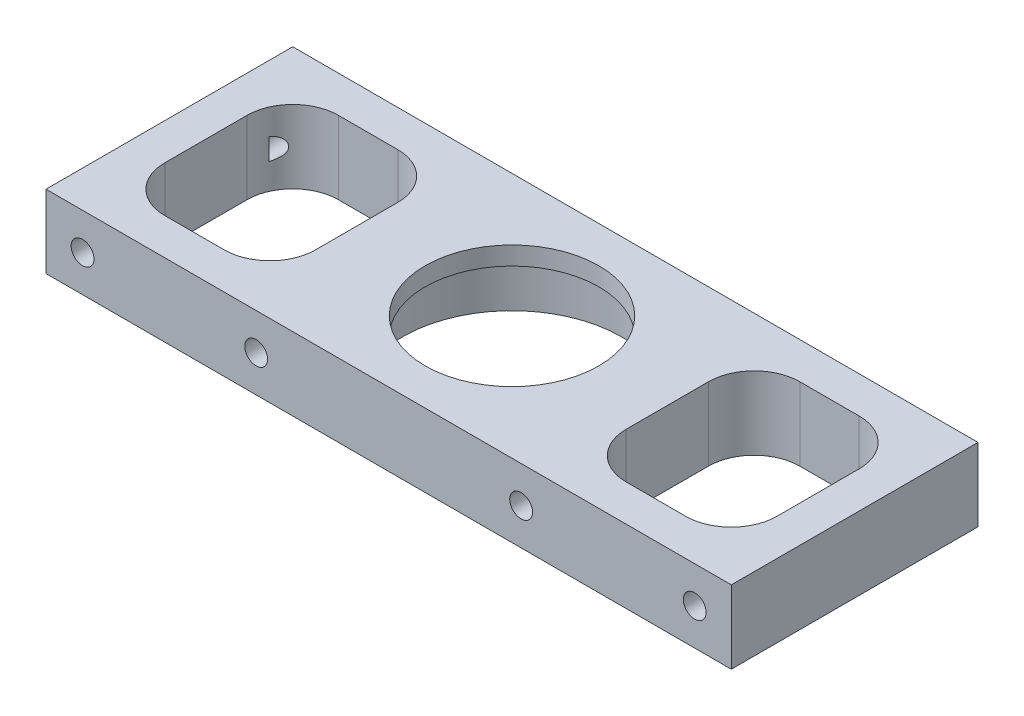
SolidWorks part; units mm, degrees
ref_plane "Спереди" through (0, 0, 0) normal (0, 0, 1) x (1, 0, 0)
ref_plane "Сверху" through (0, 0, 0) normal (0, 1, 0) x (1, 0, 0)
ref_plane "Справа" through (0, 0, 0) normal (1, 0, 0) x (0, 0, -1)
sketch "Эскиз1" plane through (0, 0, 0) normal (0, 1, 0) x (1, 0, 0)
  line L0 (37.5, 13.5) -> (37.5, -13.5)
  line L1 (-37.5, -13.5) -> (37.5, -13.5)
  line L2 (-37.5, -13.5) -> (-37.5, 13.5)
  line L3 (-37.5, 13.5) -> (37.5, 13.5)
  line L5 (-37.5, -13.5) -> (37.5, 13.5) construction
  line L6 (-37.5, 13.5) -> (37.5, -13.5) construction
  line L10 (-33.5, -9.5) -> (-33.5, 9.5) construction
  line L11 (-33.5, 9.5) -> (-17, 9.5) construction
  line L12 (-17, 9.5) -> (-17, -9.5) construction
  line L13 (-17, -9.5) -> (-33.5, -9.5) construction
  line L14 (0, -23.2365) -> (0, 25.4669) construction
  line L15 (-28.5, 9.5) -> (-22, 9.5)
  line L16 (-33.5, 4.5) -> (-33.5, -4.5)
  line L17 (-28.5, -9.5) -> (-22, -9.5)
  line L18 (-17, 4.5) -> (-17, -4.5)
  line L19 (28.5, 9.5) -> (22, 9.5)
  line L20 (17, 4.5) -> (17, -4.5)
  line L21 (33.5, 4.5) -> (33.5, -4.5)
  line L22 (28.5, -9.5) -> (22, -9.5)
  circle A0 centre (0, 0) radius 9.5
  arc A2 (17, -4.5) -> (22, -9.5) centre (22, -4.5) ccw
  arc A3 (28.5, -9.5) -> (33.5, -4.5) centre (28.5, -4.5) ccw
  arc A4 (33.5, 4.5) -> (28.5, 9.5) centre (28.5, 4.5) ccw
  arc A5 (22, 9.5) -> (17, 4.5) centre (22, 4.5) ccw
  arc A6 (-33.5, 4.5) -> (-28.5, 9.5) centre (-28.5, 4.5) cw
  arc A7 (-17, 4.5) -> (-22, 9.5) centre (-22, 4.5) ccw
  arc A8 (-22, -9.5) -> (-17, -4.5) centre (-22, -4.5) ccw
  arc A9 (-28.5, -9.5) -> (-33.5, -4.5) centre (-28.5, -4.5) cw
  point P0 (0, 0)
  point P18 (37.5, -4)
  point P27 (17, -9.5)
  point P30 (33.5, -9.5)
  point P33 (33.5, 9.5)
  point P36 (17, 9.5)
  dimension "D3" = 19
  dimension "D13" = 5
  dimension "D1" = 75
  dimension "D2" = 27
  dimension "D8" = 4
  dimension "D9" = 4
  dimension "D10" = 4
  dimension "D11" = 17
extrude "Бобышка-Вытянуть1" add sketch "Эскиз1" along normal blind 8
sketch "Эскиз9" plane through (0, 0, 0) normal (0, -1, 0) x (1, 0, 0)
  circle A0 centre (0, 0) radius 12
  dimension "D1" = 24
extrude "Вырез-Вытянуть7" cut sketch "Эскиз9" against normal blind 6
sketch "Эскиз11" plane through (0, 0, -13.5) normal (0, 0, -1) x (-1, 0, 0)
  line L1 (0, 14.6897) -> (0, -16.0991) construction
  circle A0 centre (14.5, 4) radius 1.25
  circle A1 centre (33.5, 4) radius 1.25
  circle A2 centre (-33.5, 4) radius 1.25
  circle A3 centre (-14.5, 4) radius 1.25
  dimension "D1" = 2.5
  dimension "D2" = 2.5
  dimension "D3" = 4
  dimension "D4" = 4
  dimension "D5" = 14.5
  dimension "D6" = 33.5
extrude "Вырез-Вытянуть8" cut sketch "Эскиз11" against normal blind 7
sketch "Эскиз12" plane through (0, 0, 13.5) normal (0, 0, 1) x (1, 0, 0)
  line L0 (-37.5, 0) -> (37.5, 0) construction
  line L1 (0, 40.9407) -> (0, -30.1682) construction
  circle A0 centre (-14.5, 4) radius 1.25
  circle A1 centre (-33.5, 4) radius 1.25
  circle A2 centre (14.5, 4) radius 1.25
  circle A3 centre (33.5, 4) radius 1.25
  point P4 (0, 0)
  dimension "D5" = 2.5
  dimension "D6" = 2.5
  dimension "D1" = 14.5
  dimension "D2" = 33.5
  dimension "D3" = 4
  dimension "D4" = 4
extrude "Вырез-Вытянуть9" cut sketch "Эскиз12" against normal blind 7
sketch "Эскиз13" plane through (0, 0, 0) normal (0, -1, 0) x (1, 0, 0)
  line L0 (0, 0) -> (0, 18.233) construction
  line L1 (0, 18.233) -> (0, -17.6078) construction
  line L2 (0, 0) -> (-16.7136, 0) construction
  line L3 (-16.7136, 0) -> (16.3298, 0) construction
  circle A0 centre (-11.2938, 9.0834) radius 1.25
  circle A1 centre (11.2938, 9.0834) radius 1.25
  circle A2 centre (11.2938, -9.0834) radius 1.25
  circle A3 centre (-11.2938, -9.0834) radius 1.25
  dimension "D1" = 2.5
extrude "Вырез-Вытянуть10" cut sketch "Эскиз13" against normal blind 6
